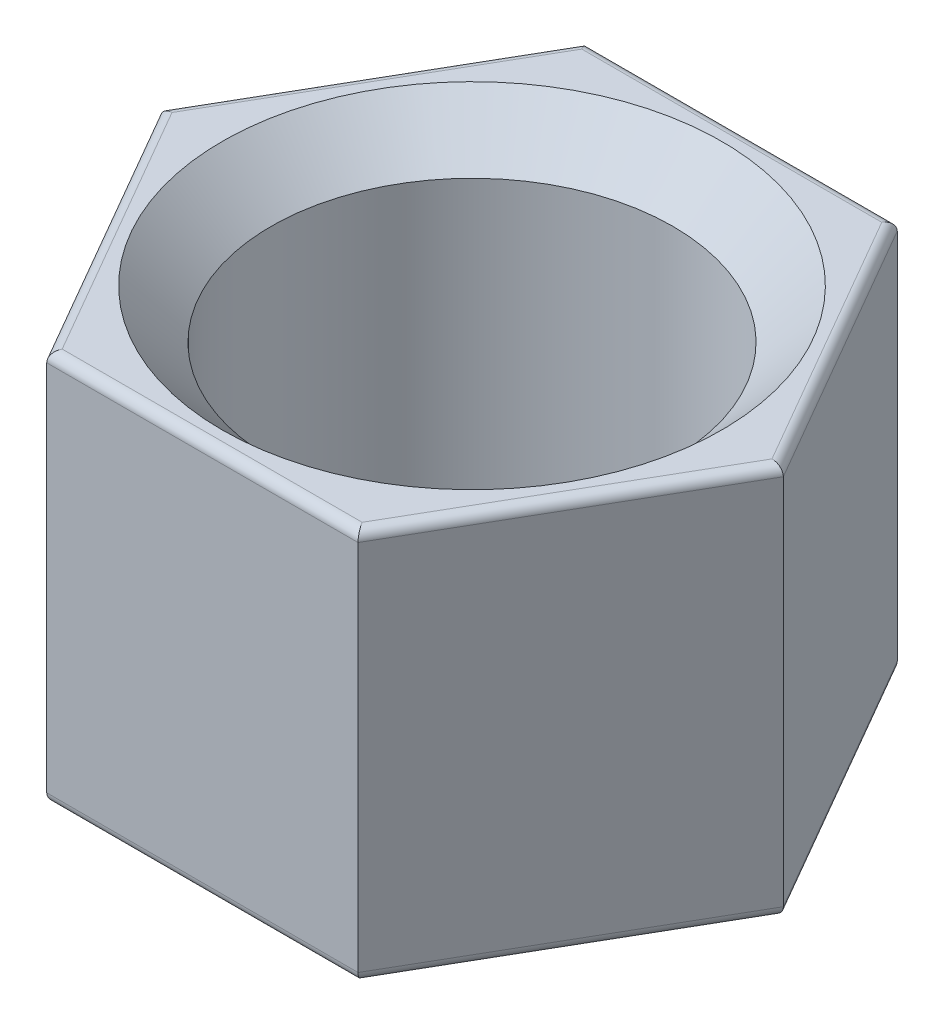
SolidWorks part; units mm, degrees
ref_plane "Front Plane" through (0, 0, 0) normal (0, 0, 1) x (1, 0, 0)
ref_plane "Top Plane" through (0, 0, 0) normal (0, 1, 0) x (1, 0, 0)
ref_plane "Right Plane" through (0, 0, 0) normal (1, 0, 0) x (0, 0, -1)
sketch "Sketch1" plane through (0, 0, 0) normal (0, 1, 0) x (1, 0, 0)
  line L1 (1.5884, 0) -> (0.7942, 1.3756)
  line L2 (0.7942, 1.3756) -> (-0.7942, 1.3756)
  line L3 (-0.7942, 1.3756) -> (-1.5884, 0)
  line L4 (-1.5884, 0) -> (-0.7942, -1.3756)
  line L5 (-0.7942, -1.3756) -> (0.7942, -1.3756)
  line L6 (0.7942, -1.3756) -> (1.5884, 0)
  point P3 (0.4388, 1.1704)
extrude "Boss-Extrude5" add sketch "Sketch1" along normal blind 2
hole_wizard "M2.5x0.45 Tapped Hole1" positions "Sketch5" profile "Sketch6" tap size "M2.5x0.45" standard "ANSI Metric" end condition through all
sketch "Sketch5" plane through (0, 2, 0) normal (0, 1, 0) x (1, 0, 0)
  point P0 (0, 0)
sketch "Sketch6" plane through (0, 2, 0) normal (1, 0, 0) x (0, 0, 1)
  line L0 (0, 0) -> (0, 2)
  line L1 (0, 2) -> (1.025, 2)
  line L2 (1.025, 2) -> (1.025, 0.25)
  line L3 (1.025, 0.25) -> (1.275, 0)
  line L5 (1.275, 0) -> (0, 0)
  line L6 (-1.025, 0.25) -> (-1.275, 0) construction
  line L11 (0, -6.35) -> (0, 107.95) construction
  dimension "Thru Tap Drill Dia." = 2.05
  dimension "Thru Tap Drill Depth" = 2
  dimension "Near C'Sink Dia." = 2.55
  dimension "Near C'Sink Angle" = 90
cosmetic thread "Hole Thread1" parameters "D2"=2.5
fillet "Fillet1" radius 0.05 6 edges at (1.1913, 2, -0.6878) (1.1913, 2, 0.6878) (0, 2, 1.3756) (-1.1913, 2, 0.6878) (0, 2, -1.3756) (-1.1913, 2, -0.6878)
fillet "Fillet2" radius 0.05 6 edges at (-1.1913, 0, -0.6878) (0, 0, -1.3756) (1.1913, 0, -0.6878) (1.1913, 0, 0.6878) (0, 0, 1.3756) (-1.1913, 0, 0.6878)
